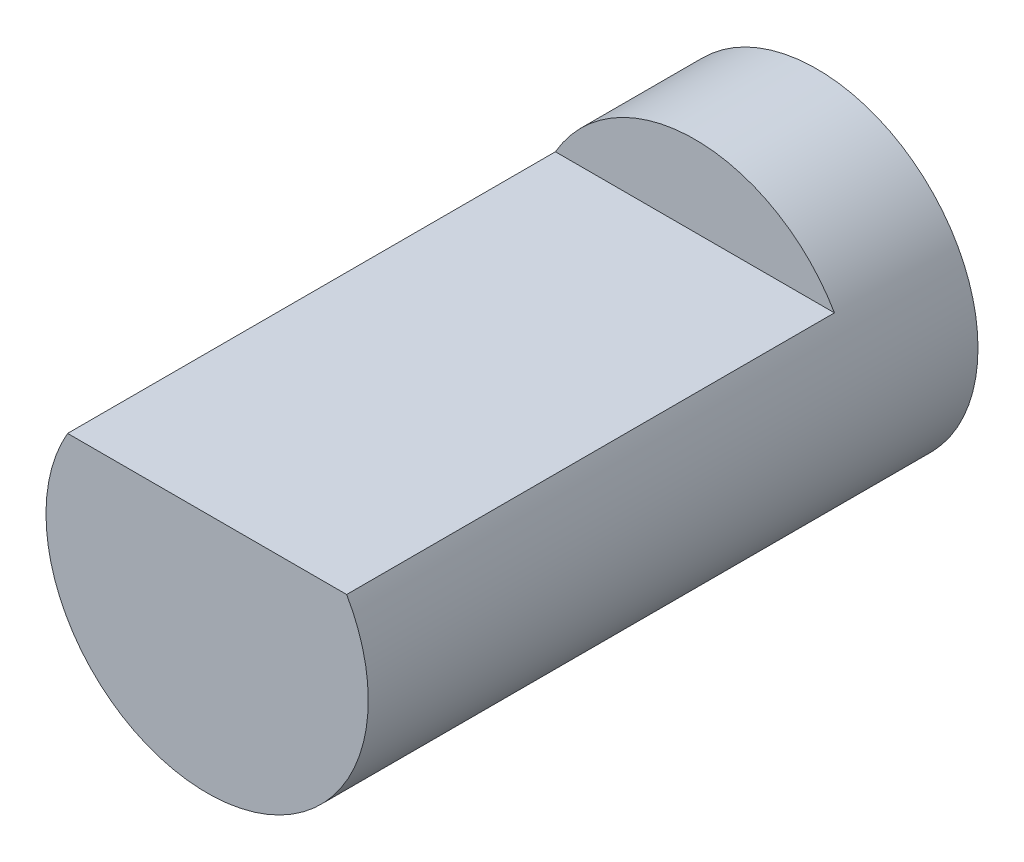
SolidWorks part; units mm, degrees
ref_plane "Front Plane" through (0, 0, 0) normal (0, 0, 1) x (1, 0, 0)
ref_plane "Top Plane" through (0, 0, 0) normal (0, 1, 0) x (1, 0, 0)
ref_plane "Right Plane" through (0, 0, 0) normal (1, 0, 0) x (0, 0, -1)
sketch "Sketch1" plane through (0, 0, 0) normal (0, 0, 1) x (1, 0, 0)
  circle A0 centre (0, 0) radius 5.2853
extrude "Boss-Extrude1" add sketch "Sketch1" along normal blind 20 contours A0
sketch "Sketch4" plane through (0, 0, 20) normal (0, 0, 1) x (1, 0, 0)
  line L0 (-4.5763, 2.6441) -> (4.5763, 2.6441)
  circle A0 centre (0, 0) radius 5.2853 construction
  arc A1 (4.5763, 2.6441) -> (-4.5763, 2.6441) centre (0, 0) ccw
extrude "Cut-Extrude8" cut sketch "Sketch4" against normal blind 16
